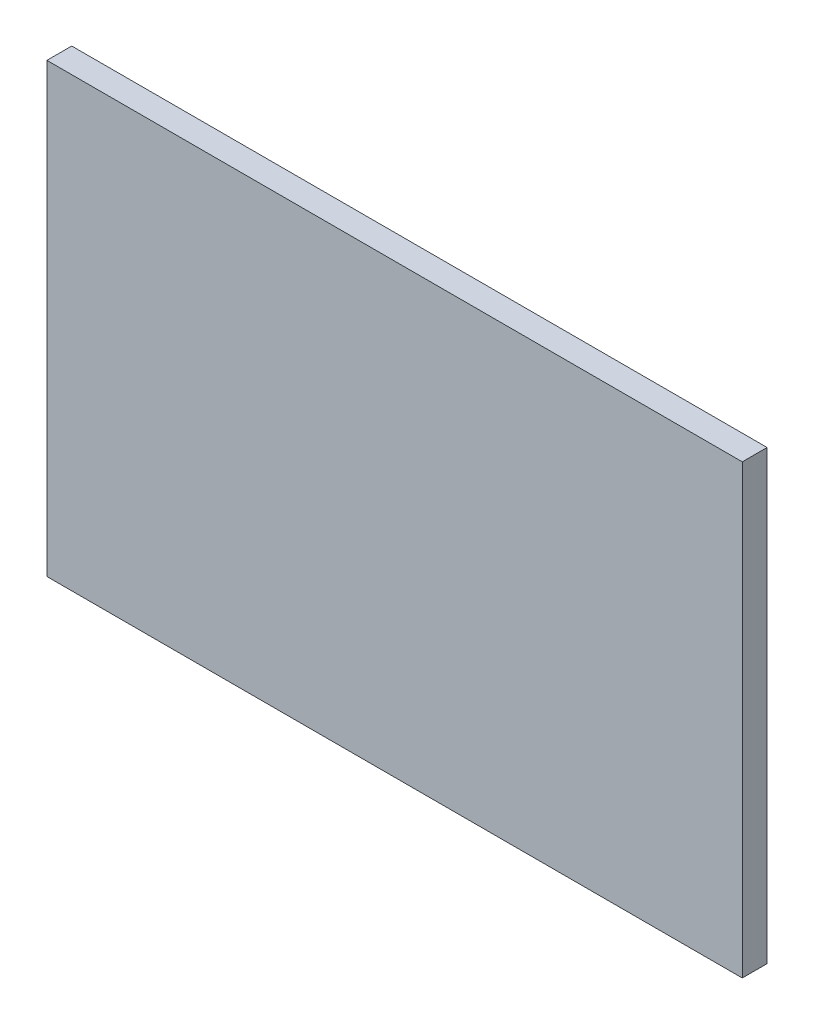
SolidWorks part; units mm, degrees
ref_plane "Front Plane" through (0, 0, 0) normal (0, 0, 1) x (1, 0, 0)
ref_plane "Top Plane" through (0, 0, 0) normal (0, 1, 0) x (1, 0, 0)
ref_plane "Right Plane" through (0, 0, 0) normal (1, 0, 0) x (0, 0, -1)
sketch "Sketch1" plane through (0, 0, 0) normal (0, 0, 1) x (1, 0, 0)
  line L1 (0, 0) -> (88.9, 0)
  line L2 (0, 0) -> (0, 57.15)
  line L3 (0, 57.15) -> (88.9, 57.15)
  line L4 (88.9, 0) -> (88.9, 57.15)
  dimension "D1" = 88.9
  dimension "D2" = 57.15
extrude "Boss-Extrude1" add sketch "Sketch1" along normal blind 3.175
